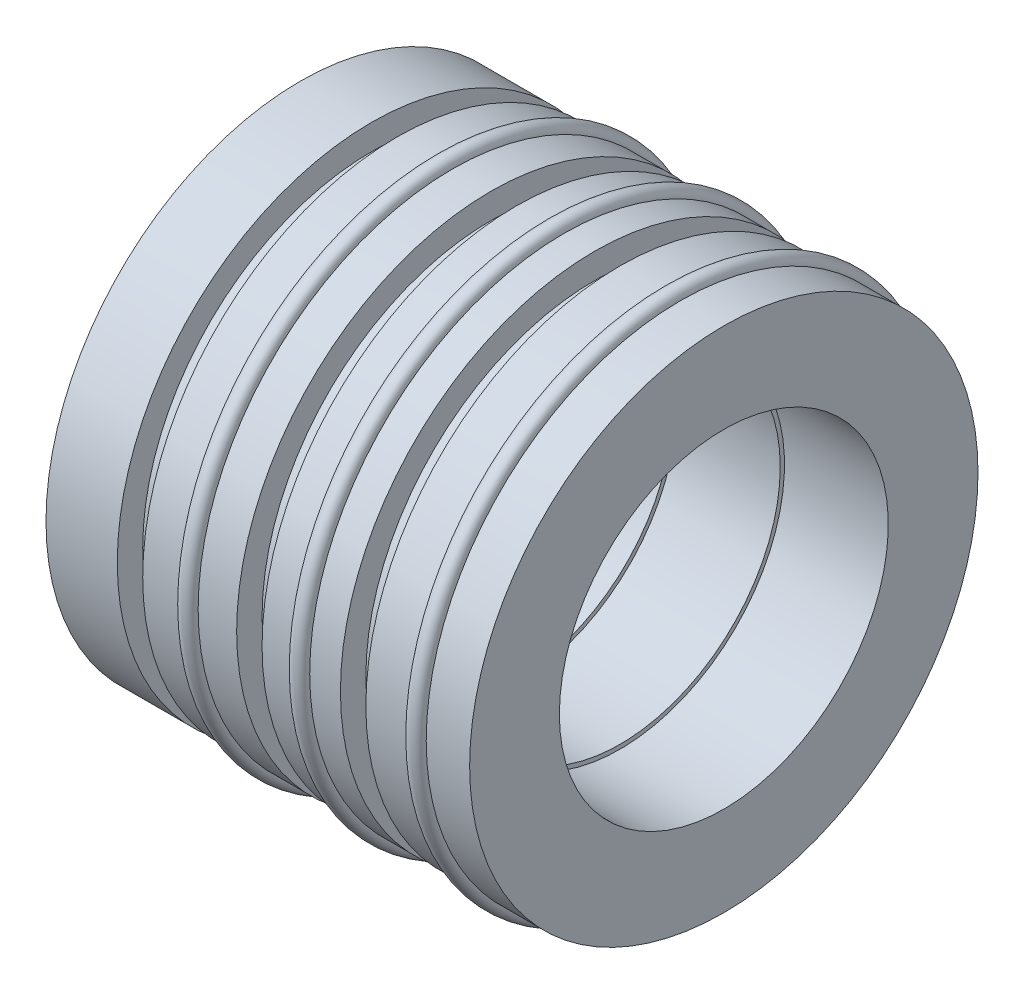
SolidWorks part; units mm, degrees
ref_plane "Front Plane" through (0, 0, 0) normal (0, 0, 1) x (1, 0, 0)
ref_plane "Top Plane" through (0, 0, 0) normal (0, 1, 0) x (1, 0, 0)
ref_plane "Right Plane" through (0, 0, 0) normal (1, 0, 0) x (0, 0, -1)
sketch "Sketch1" plane through (0, 0, 0) normal (0, 0, 1) x (1, 0, 0)
  line L0 (0, 0) -> (36.5459, 0) construction
  line L1 (6.378, 9.3528) -> (6.378, 15.24)
  line L3 (31.778, 15.24) -> (31.778, 9.8608)
  line L4 (31.778, 9.8608) -> (25.555, 9.8608)
  line L5 (25.555, 9.8608) -> (25.555, 9.6068)
  line L6 (25.555, 9.6068) -> (19.332, 9.6068)
  line L7 (19.332, 9.6068) -> (19.332, 9.3528)
  line L8 (19.332, 9.3528) -> (13.109, 9.3528)
  line L24 (10.6522, 15.24) -> (10.6522, 13.716)
  line L25 (10.6522, 13.716) -> (12.1762, 13.716)
  line L26 (12.1762, 13.716) -> (12.1762, 15.24)
  line L27 (12.1762, 15.24) -> (14.4841, 15.24)
  line L28 (17.808, 15.24) -> (17.808, 13.716)
  line L29 (17.808, 13.716) -> (19.332, 13.716)
  line L30 (19.332, 13.716) -> (19.332, 15.24)
  line L31 (19.332, 15.24) -> (21.1735, 15.24)
  line L32 (24.031, 15.24) -> (24.031, 13.716)
  line L33 (24.031, 13.716) -> (25.555, 13.716)
  line L34 (25.555, 13.716) -> (25.555, 15.24)
  line L35 (25.555, 15.24) -> (28.1585, 15.24)
  line L38 (6.378, 15.24) -> (10.6522, 15.24)
  line L39 (15.5001, 15.24) -> (17.808, 15.24)
  line L40 (22.1895, 15.24) -> (24.031, 15.24)
  line L41 (29.1745, 15.24) -> (31.778, 15.24)
  line L45 (14.4841, 15.24) -> (15.5001, 15.24) construction
  line L46 (21.1735, 15.24) -> (22.1895, 15.24) construction
  line L47 (28.1585, 15.24) -> (29.1745, 15.24) construction
  line L48 (13.109, 9.3528) -> (6.378, 9.3528)
  arc A9 (22.1895, 15.24) -> (21.1735, 15.24) centre (21.6815, 15.24) ccw
  arc A10 (15.5001, 15.24) -> (14.4841, 15.24) centre (14.9921, 15.24) ccw
  arc A14 (29.1745, 15.24) -> (28.1585, 15.24) centre (28.6665, 15.24) ccw
  point P9 (4.5035, 15.24)
  point P13 (-1.7258, 15.24)
  point P14 (-7.56, 15.24)
  point P15 (12.1762, 14.478)
  dimension "D8" = 0.508
  dimension "D4" = 15.24
  dimension "D10" = 1.524
  dimension "D11" = 1.524
  dimension "D3" = 6.223
  dimension "D2" = 0.254
  dimension "D5" = 9.8608
  dimension "D6" = 1.524
  dimension "D7" = 1.524
  dimension "D9" = 19.6018
  dimension "D12" = 25.4
revolve "Revolve1" add sketch "Sketch1" angle 360 about L0
ref_plane "Plane3" through (11.4142, 0, 0) normal (1, 0, 0) x (0, 0, -1)
ref_plane "Plane4" through (18.57, 0, 0) normal (-1, 0, 0) x (0, 0, 1)
ref_plane "Plane5" through (24.793, 0, 0) normal (1, 0, 0) x (0, 0, -1)
sketch "Sketch6" plane through (11.4142, 0, 0) normal (1, 0, 0) x (0, 0, -1)
  point P0 (0, 0)
sketch "Sketch8" plane through (24.793, 0, 0) normal (1, 0, 0) x (0, 0, -1)
  point P0 (0, 0)
equation "\"kero_radius\"=0.334in"
equation "\"lox_radius\"=0.23622in"
equation "\"Cavity_width\"=0.031in"
equation "\"tooth_width\"=0.01in"
equation "\"cavity_depth\"=0.031in"
equation "\"seal_step\"=0.01in"
equation "\"purge_length\"=0.04in"
equation "\"insert_radius\" = 0.6in"
equation "\"recycle_groove width\" = 0.06in"
equation "\"recycle_groove_depth\" = 0.06in"
equation "\"N2_purge_width\"= .06in"
equation "\"N2_purge_depth\"= .06in"
equation "\"drain_width\"= .06in"
equation "\"drain_depth\"= .06in"
equation "\"D10@Sketch1\"=\"N2_purge_depth\""
equation "\"D11@Sketch1\"=\"N2_purge_width\""
equation "\"radial_clearance\"= .002in"
equation "\"InsertLength\"= 1in"
equation "\"D4@Sketch1\"=\"insert_radius\""
equation "\"bumb_radius\"=0.02"
equation "\"bearing_radius\"= 0.629921"
equation "\"bearing_width\"=0.393701"
equation "\"IPS_flange_width\"= .25in"
equation "\"IPS_flange_radius\" = 1.4in"
equation "\"IPS_LOX_male_radius\"= .9in"
equation "\"IPS_Kero_male_radius\" = .9in"
equation "\"IPS_radius\"= .95in"
equation "\"D3@Sketch1\"=5*\"tooth_width\"+5*\"Cavity_width\"+\"purge_length\""
equation "\"D2@Sketch1\"=\"seal_step\""
equation "\"D5@Sketch1\"=\"lox_radius\"+.15+\"radial_clearance\""
equation "\"D6@Sketch1\"=\"drain_width\""
equation "\"D7@Sketch1\"=\"drain_depth\""
equation "\"D8@Sketch1\"=\"bumb_radius\""
equation "\"D12@Sketch1\"=\"InsertLength\""
